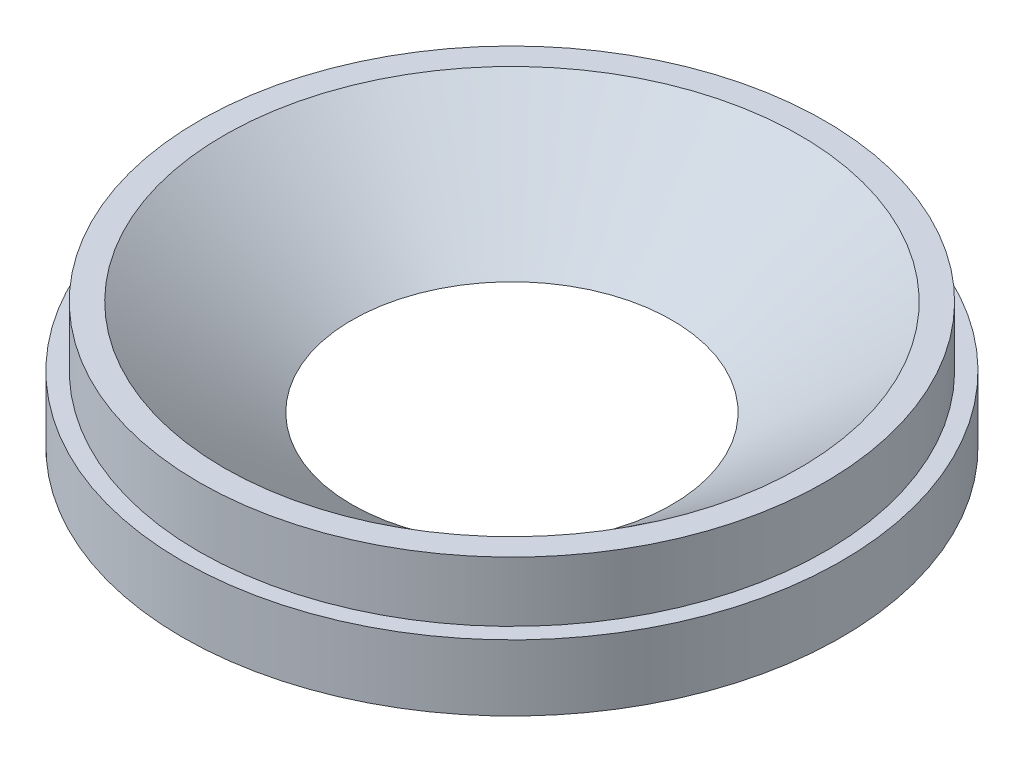
SolidWorks part; units mm, degrees
material "Phenolic Rod Stock"
ref_plane "Front Plane" through (0, 0, 0) normal (0, 0, 1) x (1, 0, 0)
ref_plane "Top Plane" through (0, 0, 0) normal (0, 1, 0) x (1, 0, 0)
ref_plane "Right Plane" through (0, 0, 0) normal (1, 0, 0) x (0, 0, -1)
sketch "Sketch1" plane through (0, 0, 0) normal (0, 0, 1) x (1, 0, 0)
  line L0 (0, 28.574) -> (0, 0) construction
  line L1 (0, 0) -> (-16.9379, 0) construction
  line L3 (-16.9379, 0) -> (-30.4943, 10.16)
  line L5 (-33.147, 3.81) -> (-34.8996, 3.81)
  line L7 (-25.4, 0) -> (-16.9379, 0)
  line L8 (-16.9379, 0) -> (-10.6911, -4.6817) construction
  line L9 (-34.8996, 3.81) -> (-34.8996, -3.175)
  line L10 (-34.8996, -3.175) -> (-25.4, -3.175)
  line L11 (-25.4, -3.175) -> (-25.4, 0)
  line L12 (-33.147, 3.81) -> (-33.147, 10.16)
  line L13 (-33.147, 10.16) -> (-30.4943, 10.16)
  arc A0 (-10.6911, -4.6817) -> (-6.6802, -12.7) centre (-16.7005, -12.7) cw construction
  dimension "D6" = 10.0203
  dimension "D3" = 53.15
  dimension "D2" = 6.6802
  dimension "D7" = 12.7
  dimension "D1" = 34.8996
  dimension "D8" = 3.175
  dimension "D9" = 25.4
  dimension "D4" = 33.147
  dimension "D5" = 6.35
  dimension "D10" = 10.16
revolve "Revolve1" add sketch "Sketch1" angle 360 about L0
equation "\"D6@Sketch1\"=\"D2@Sketch1\"*1.5"
